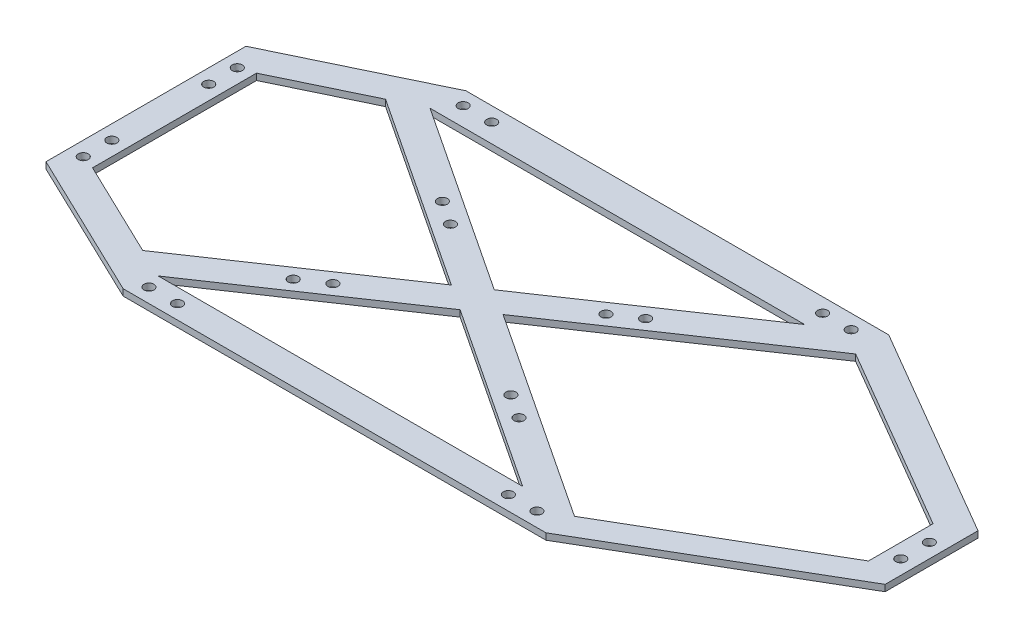
SolidWorks part; units mm, degrees
ref_plane "Front Plane" through (0, 0, 0) normal (0, 0, 1) x (1, 0, 0)
ref_plane "Top Plane" through (0, 0, 0) normal (0, 1, 0) x (1, 0, 0)
ref_plane "Right Plane" through (0, 0, 0) normal (1, 0, 0) x (0, 0, -1)
sketch "Sketch1" plane through (0, 0, 0) normal (0, 1, 0) x (1, 0, 0)
  line L0 (0, 0) -> (0, 120)
  line L1 (0, 120) -> (150, 32.5)
  line L2 (150, 32.5) -> (150, -32.5)
  line L3 (150, -32.5) -> (0, -120)
  line L4 (0, -120) -> (0, 0)
  line L5 (0, 120) -> (-296, 120)
  line L6 (-296, 120) -> (-400, 70)
  line L7 (-400, 70) -> (-400, -70)
  line L8 (-400, -70) -> (-296, -120)
  line L9 (-296, -120) -> (0, -120)
  line L10 (0, 0) -> (150, 0)
  line L11 (0, 0) -> (-400, 0)
  line L12 (-380, 57.424) -> (-298.0025, 96.8459)
  line L13 (-298.0025, 96.8459) -> (0, 96.8459)
  line L14 (0, 96.8459) -> (130, 21.0126)
  line L15 (130, 21.0126) -> (130, -24.1667)
  line L16 (130, -24.1667) -> (0, -100)
  line L17 (0, -100) -> (-291.442, -100)
  line L18 (-291.442, -100) -> (-380, -57.424)
  line L19 (-380, -57.424) -> (-380, 57.424)
  line L20 (-298.0025, 96.8459) -> (0, -100)
  line L21 (0, 96.8459) -> (-291.442, -100)
  line L22 (-319.0039, 86.7491) -> (-36.2869, -100)
  line L23 (-312.3162, -89.9643) -> (-35.7326, 96.8459)
  dimension "D1" = 400
  dimension "D2" = 150
  dimension "D3" = 65
  dimension "D4" = 104
  dimension "D5" = 140
  dimension "D6" = 87.5
  dimension "D7" = 20
  dimension "D8" = 20
  dimension "D9" = 20
  dimension "D10" = 20
  dimension "D11" = 20
  dimension "D12" = 20
  dimension "D13" = 20
  dimension "D14" = 20
extrude "Boss-Extrude3" add sketch "Sketch1" along normal blind 4.5 contours L22 L23 L11 | L23 L11 L20 | L23 L22 L21 L20 L11 | L21 L11 L20 | L23 L20 L11 L21 L13 | L21 L22 L17 L20 | L11 L23 L20 L12 L22 | L23 L18 L21 L22 | L18 L19 L11 L7 L8 L9 L4 L17 | L15 L16 L4 L3 L2 L10 | L14 L15 L10 L2 L1 L0 | L11 L19 L12 L13 L0 L5 L6 L7
sketch "Sketch2" plane through (0, 4.5, 0) normal (0, 1, 0) x (1, 0, 0)
  line L0 (-36.2869, -110) -> (-16.2869, -110)
  line L1 (-36.2869, -100) -> (-36.2869, -110)
  circle A0 centre (-16.2869, -110) radius 3.5
  circle A1 centre (-36.2869, -110) radius 3.5
  dimension "D1" = 7
  dimension "D2" = 7
  dimension "D3" = 10
  dimension "D4" = 20
extrude "Cut-Extrude2" cut sketch "Sketch2" against normal blind 4.5
mirror "Mirror1" about plane through (0, 0, 0) normal (0, 0, 1) of "Cut-Extrude2"
sketch "Sketch3" plane through (0, 4.5, 0) normal (0, 1, 0) x (1, 0, 0)
  line L0 (-287.942, -110) -> (-267.942, -110)
  line L1 (-267.942, -110) -> (-267.942, -100)
  line L2 (-36.2869, -100) -> (-291.442, -100) construction
  line L3 (-291.442, -100) -> (-291.442, -110)
  circle A0 centre (-287.942, -110) radius 3.5
  circle A1 centre (-267.942, -110) radius 3.5
  dimension "D2" = 7
  dimension "D3" = 7
  dimension "D1" = 10
  dimension "D4" = 20
extrude "Cut-Extrude3" cut sketch "Sketch3" against normal blind 4.5
mirror "Mirror2" about plane through (0, 0, 0) normal (0, 0, 1) of "Cut-Extrude3"
sketch "Sketch4" plane through (0, 4.5, 0) normal (0, 1, 0) x (1, 0, 0)
  line L0 (140, 8.423) -> (140, -11.577)
  line L1 (140, -1.577) -> (130, -1.577)
  line L2 (130, 21.0126) -> (130, -24.1667) construction
  circle A0 centre (140, 8.423) radius 3.5
  circle A1 centre (140, -11.577) radius 3.5
  dimension "D1" = 7
  dimension "D2" = 7
  dimension "D3" = 10
  dimension "D4" = 20
extrude "Cut-Extrude4" cut sketch "Sketch4" against normal blind 4.5
sketch "Sketch5" plane through (0, 4.5, 0) normal (0, 1, 0) x (1, 0, 0)
  line L0 (-380, 57.424) -> (-390, 57.424)
  line L1 (-390, 53.924) -> (-390, 33.924)
  circle A0 centre (-390, 53.924) radius 3.5
  circle A1 centre (-390, 33.924) radius 3.5
  dimension "D2" = 7
  dimension "D3" = 7
  dimension "D1" = 10
  dimension "D4" = 20
extrude "Cut-Extrude5" cut sketch "Sketch5" against normal blind 4.5
mirror "Mirror3" about plane through (0, 0, 0) normal (0, 0, 1) of "Cut-Extrude5"
sketch "Sketch6" plane through (0, 4.5, 0) normal (0, 1, 0) x (1, 0, 0)
  line L0 (-220.5289, 33.686) -> (-237.2169, 44.7092)
  line L1 (-237.2169, 44.7092) -> (-231.7053, 53.0532)
  line L2 (-298.0025, 96.8459) -> (-165.408, 9.2605) construction
  circle A0 centre (-237.2169, 44.7092) radius 3.5
  circle A1 centre (-220.5289, 33.686) radius 3.5
  dimension "D3" = 7
  dimension "D4" = 7
  dimension "D1" = 10
  dimension "D2" = 20
extrude "Cut-Extrude6" cut sketch "Sketch6" against normal blind 4.5
sketch "Sketch7" plane through (0, 4.5, 0) normal (0, 1, 0) x (1, 0, 0)
  line L0 (-247.8329, -46.4109) -> (-242.2358, -54.6978)
  line L1 (-312.3162, -89.9643) -> (-183.3496, -2.8576) construction
  line L2 (-242.2358, -54.6978) -> (-225.662, -43.5036)
  circle A0 centre (-242.2358, -54.6978) radius 3.5
  circle A1 centre (-225.662, -43.5036) radius 3.5
  dimension "D3" = 7
  dimension "D4" = 7
  dimension "D1" = 10
  dimension "D2" = 20
extrude "Cut-Extrude7" cut sketch "Sketch7" against normal blind 4.5
sketch "Sketch8" plane through (0, 4.5, 0) normal (0, 1, 0) x (1, 0, 0)
  line L0 (-100.5703, 53.0532) -> (-94.9732, 44.7663)
  line L1 (-165.408, 9.2605) -> (-35.7326, 96.8459) construction
  line L2 (-94.9732, 44.7663) -> (-111.547, 33.5721)
  circle A0 centre (-94.9732, 44.7663) radius 3.5
  circle A1 centre (-111.547, 33.5721) radius 3.5
  point P7 (-100.5703, 53.0532)
  dimension "D3" = 7
  dimension "D4" = 7
  dimension "D1" = 10
  dimension "D2" = 20
extrude "Cut-Extrude8" cut sketch "Sketch8" against normal blind 4.5
sketch "Sketch9" plane through (0, 4.5, 0) normal (0, 1, 0) x (1, 0, 0)
  line L0 (-73.6714, -51.3362) -> (-79.1831, -59.6802)
  line L1 (-147.3429, -2.6725) -> (0, -100) construction
  line L2 (-79.1831, -59.6802) -> (-95.871, -48.657)
  circle A0 centre (-95.871, -48.657) radius 3.5
  circle A1 centre (-79.1831, -59.6802) radius 3.5
  dimension "D3" = 7
  dimension "D4" = 7
  dimension "D1" = 10
  dimension "D2" = 20
extrude "Cut-Extrude9" cut sketch "Sketch9" against normal blind 4.5
